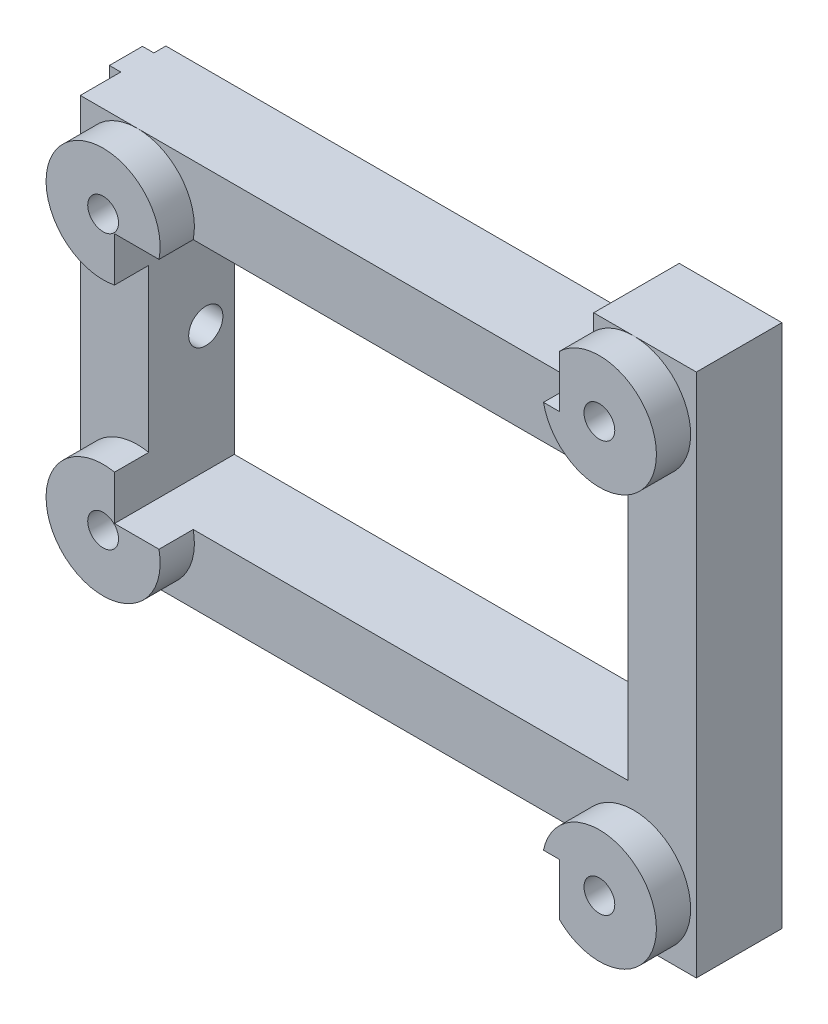
SolidWorks part; units mm, degrees
ref_plane "Plan de face" through (0, 0, 0) normal (0, 0, 1) x (1, 0, 0)
ref_plane "Plan de dessus" through (0, 0, 0) normal (0, 1, 0) x (1, 0, 0)
ref_plane "Plan de droite" through (0, 0, 0) normal (1, 0, 0) x (0, 0, -1)
sketch "Esquisse1" plane through (0, 0, 0) normal (0, 0, 1) x (1, 0, 0)
  line L1 (-27, -23) -> (27, -23)
  line L2 (-27, -23) -> (-27, 23)
  line L3 (-27, 23) -> (27, 23)
  line L4 (27, -23) -> (27, 23)
  point P7 (0, -23)
  point P8 (-27, 0)
  dimension "D1" = 46
  dimension "D2" = 54
extrude "Main" add sketch "Esquisse1" along normal blind 7.5
sketch "Esquisse2" plane through (0, 0, 7.5) normal (0, 0, 1) x (1, 0, 0)
  line L1 (-27, -23) -> (27, -23) construction
  line L2 (27, 23) -> (-27, 23) construction
  line L3 (-27, 23) -> (-27, -23) construction
  circle A0 centre (-22, -12) radius 1.35
  circle A1 centre (-22, 12) radius 1.35
  circle A2 centre (21.5, 18) radius 1.35
  circle A3 centre (21.5, -18) radius 1.35
  dimension "D1" = 2.7
  dimension "D2" = 48.5
  dimension "D3" = 5
  dimension "D4" = 11
  dimension "D5" = 11
  dimension "D6" = 5
  dimension "D7" = 5
  dimension "D8" = 24
  dimension "D9" = 36
extrude "UsbFixHoles" cut sketch "Esquisse2" against normal through all
sketch "Esquisse3" plane through (0, 0, 7.5) normal (0, 0, 1) x (1, 0, 0)
  circle A0 centre (-22, 12) radius 5
  circle A1 centre (-22, -12) radius 5
  circle A2 centre (21.5, -18) radius 5
  circle A3 centre (21.5, 18) radius 5
  circle A4 centre (21.5, 18) radius 1.35 construction
  circle A5 centre (-22, 12) radius 1.35 construction
  circle A6 centre (-22, -12) radius 1.35 construction
  circle A7 centre (21.5, -18) radius 1.35 construction
  dimension "D1" = 10
extrude "CircleSupport" add sketch "Esquisse3" along normal blind 3
sketch "Esquisse4" plane through (0, -23, 0) normal (0, -1, 0) x (1, 0, 0)
  line L1 (18, 10.5) -> (-27, 10.5)
  line L2 (18, 10.5) -> (18, 0)
  line L3 (18, 0) -> (-27, 0)
  line L4 (-27, 10.5) -> (-27, 0)
  line L5 (26.5, 10.5) -> (16.5, 10.5) construction
  point P4 (18, 13.754)
  dimension "D2" = 45
extrude "SideCutoff" cut sketch "Esquisse4" against normal blind 6
sketch "Esquisse6" plane through (0, 23, 0) normal (0, 1, 0) x (1, 0, 0)
  line L0 (27, -7.5) -> (27, 0) construction
  line L1 (-27, 0) -> (18, 0)
  line L2 (-27, 0) -> (-27, -10.5)
  line L3 (-27, -10.5) -> (18, -10.5)
  line L4 (18, 0) -> (18, -10.5)
  line L7 (27, 0) -> (-27, 0) construction
  line L8 (16.5, -10.5) -> (26.5, -10.5) construction
  point P4 (0, 0)
  point P7 (18, -7.5)
  point P8 (18, 0)
  point P11 (18, -10.0965)
  point P14 (-26.2475, -10.5)
  point P16 (-27, 0)
  dimension "D1" = 9
extrude "SideLeftCutoff" cut sketch "Esquisse6" against normal blind 6
sketch "Esquisse7" plane through (-27, 0, 0) normal (-1, 0, 0) x (0, 0, 1)
  line L0 (7.5, 12) -> (7.5, -12) construction
  line L1 (1.05, 17) -> (3.95, 17)
  line L2 (1.05, 17) -> (1.05, -17)
  line L3 (1.05, -17) -> (3.95, -17)
  line L4 (3.95, 17) -> (3.95, -17)
  line L9 (0, 17) -> (7.5, 17) construction
  line L10 (7.5, -17) -> (0, -17) construction
  point P4 (2.5, 17)
  point P8 (2.0446, 17)
  point P10 (3.75, 17)
  point P11 (4.4583, 17)
  dimension "D1" = 2.9
  dimension "D2" = 3.55
extrude "MakerBeamFixShaft" add sketch "Esquisse7" along normal blind 1
sketch "Esquisse10" plane through (0, 0, 10.5) normal (0, 0, 1) x (1, 0, 0)
  line L1 (-21, 11) -> (21, 11)
  line L2 (-21, 11) -> (-21, -11)
  line L3 (-21, -11) -> (21, -11)
  line L4 (21, 11) -> (21, -11)
  line L6 (-27, -17) -> (-27, 17) construction
  line L7 (27, -23) -> (27, 23) construction
  line L8 (-22, -17) -> (16.601, -17) construction
  line L9 (-22, 17) -> (16.601, 17) construction
  dimension "D1" = 6
  dimension "D2" = 6
  dimension "D3" = 6
  dimension "D4" = 6
extrude "CentralHole" cut sketch "Esquisse10" against normal through all both and the other way through all
sketch "Esquisse8" plane through (-28, 0, 0) normal (-1, 0, 0) x (0, 0, 1)
  line L0 (3.95, 17) -> (1.05, 17) construction
  line L2 (3.95, -17) -> (3.95, 17) construction
  circle A0 centre (2.5, 0) radius 1.5
  point P7 (2.5, 17)
  point P12 (3.95, 0)
  dimension "D1" = 3
extrude "VerticalFixHole" cut sketch "Esquisse8" against normal up to next
sketch "Esquisse11" plane through (0, 0, 7.5) normal (0, 0, -1) x (-1, 0, 0)
  circle A0 centre (-21.5, 18) radius 1.35
  circle A1 centre (22, 12) radius 1.35
  circle A2 centre (22, -12) radius 1.35
  circle A3 centre (-21.5, -18) radius 1.35
  circle A4 centre (-21.5, -18) radius 1.35 construction
  circle A5 centre (-21.5, 18) radius 1.35 construction
  circle A6 centre (22, -12) radius 1.35 construction
  circle A7 centre (22, 12) radius 1.35 construction
extrude "UsbFixHoles2" cut sketch "Esquisse11" against normal through all
